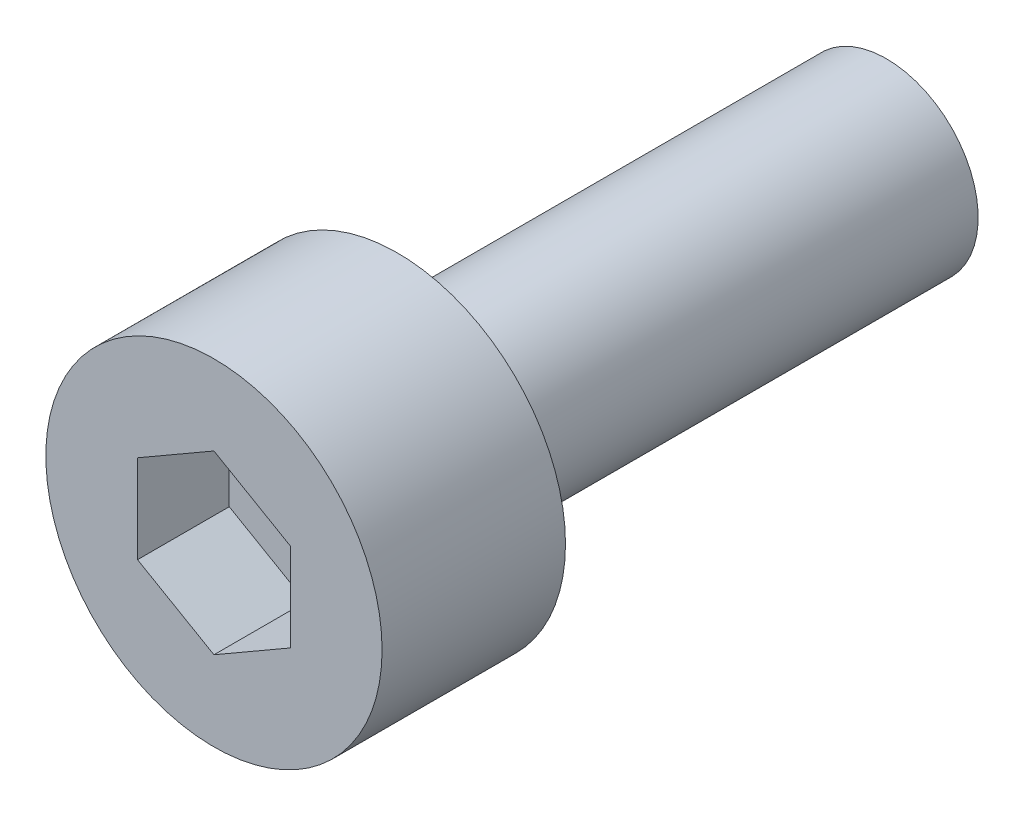
SolidWorks part; units mm, degrees
material "灰铸铁"
ref_plane "前视基准面" through (0, 0, 0) normal (0, 0, 1) x (1, 0, 0)
ref_plane "上视基准面" through (0, 0, 0) normal (0, 1, 0) x (1, 0, 0)
ref_plane "右视基准面" through (0, 0, 0) normal (1, 0, 0) x (0, 0, -1)
sketch "草图1" plane through (0, 0, 0) normal (0, 0, 1) x (1, 0, 0)
  circle A0 centre (0, 0) radius 2.75
  dimension "D1" = 5.5
extrude "凸台-拉伸1" add sketch "草图1" along normal blind 3
sketch "草图2" plane through (0, 0, 3) normal (0, 0, 1) x (1, 0, 0)
  line L1 (0, -1.4434) -> (1.25, -0.7217)
  line L2 (1.25, -0.7217) -> (1.25, 0.7217)
  line L3 (1.25, 0.7217) -> (0, 1.4434)
  line L4 (0, 1.4434) -> (-1.25, 0.7217)
  line L5 (-1.25, 0.7217) -> (-1.25, -0.7217)
  line L6 (-1.25, -0.7217) -> (0, -1.4434)
  circle A0 centre (0, 0) radius 1.25 construction
  dimension "D1" = 2.5
extrude "切除-拉伸1" cut sketch "草图2" against normal blind 1.5
sketch "草图3" plane through (0, 0, 0) normal (0, 0, -1) x (-1, 0, 0)
  circle A0 centre (0, 0) radius 1.5
extrude "凸台-拉伸2" add sketch "草图3" along normal blind 8
